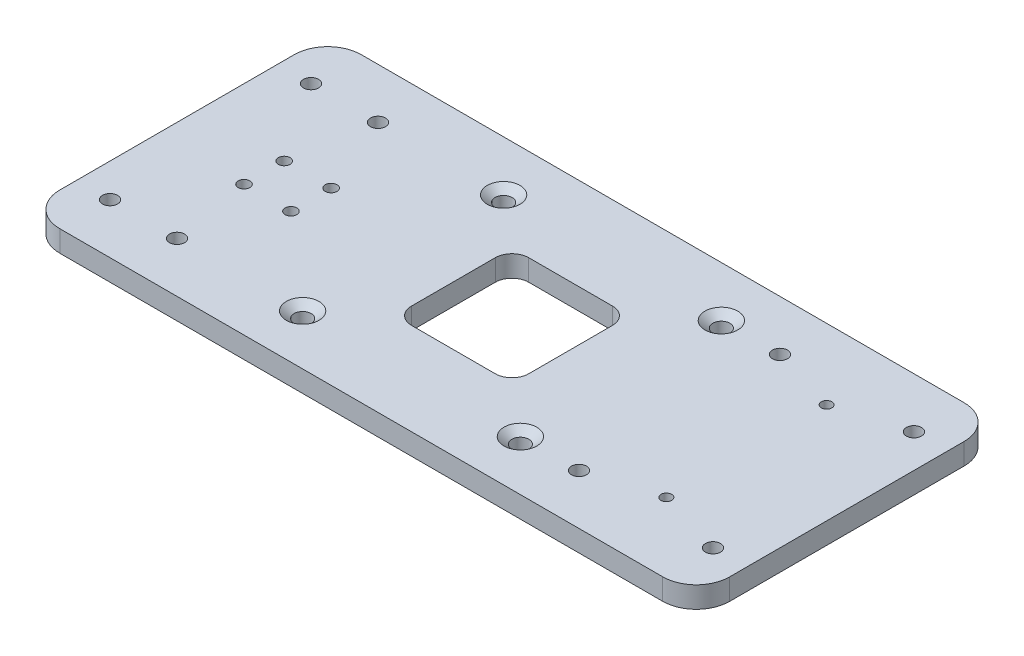
SolidWorks part; units mm, degrees
ref_plane "Front Plane" through (0, 0, 0) normal (0, 0, 1) x (1, 0, 0)
ref_plane "Top Plane" through (0, 0, 0) normal (0, 1, 0) x (1, 0, 0)
ref_plane "Right Plane" through (0, 0, 0) normal (1, 0, 0) x (0, 0, -1)
sketch "Sketch1" plane through (0, 0, 0) normal (0, 1, 0) x (1, 0, 0)
  line L1 (-100, -45) -> (100, -45)
  line L2 (-100, -45) -> (-100, 45)
  line L3 (-100, 45) -> (100, 45)
  line L4 (100, -45) -> (100, 45)
  line L5 (-100, -45) -> (100, 45) construction
  line L6 (-100, 45) -> (100, -45) construction
  point P0 (0, 0)
  dimension "D1" = 200
  dimension "D2" = 90
extrude "Boss-Extrude1" add sketch "Sketch1" along normal blind 6.35
sketch "Sketch2" plane through (0, 6.35, 0) normal (0, 1, 0) x (1, 0, 0)
  point P0 (-32.5, -30)
  point P2 (32.5, -30)
  point P5 (32.5, 30)
  point P6 (-32.5, 30)
  dimension "D1" = 30
  dimension "D2" = 32.5
  dimension "D3" = 2
  dimension "D4" = 2
hole_wizard "CSK for #10 Flat Head Machine Screw (100)1" positions "Sketch3" profile "Sketch5" countersink size "#10" standard "ANSI Inch" end condition through all
sketch "Sketch3" plane through (0, 6.35, 0) normal (0, 1, 0) x (1, 0, 0)
  point P0 (-32.5, 30)
  point P3 (-32.5, -30)
  point P6 (32.5, -30)
  point P9 (32.5, 30)
sketch "Sketch5" plane through (-32.5, 6.35, -30) normal (1, 0, 0) x (0, 0, 1)
  line L0 (0, 0) -> (0, 6.35)
  line L1 (0, 6.35) -> (2.5527, 6.35)
  line L2 (2.5527, 6.35) -> (2.5527, 1.9608)
  line L3 (2.5527, 1.9608) -> (4.8895, 0)
  line L5 (4.8895, 0) -> (0, 0)
  line L6 (-2.5527, 1.9608) -> (-4.8895, 0) construction
  line L11 (0, -6.35) -> (0, 107.95) construction
  dimension "Thru Hole Dia." = 5.1054
  dimension "Thru Hole Depth" = 6.35
  dimension "Near C'Sink Dia." = 9.779
  dimension "Near C'Sink Angle" = 100
sketch "Sketch6" plane through (0, 6.35, 0) normal (0, 1, 0) x (1, 0, 0)
  point P0 (-90, -30)
  point P1 (-70, -30)
  point P3 (50, -30)
  point P5 (90, -30)
  point P6 (90, 30)
  point P7 (-90, 30)
  point P9 (50, 30)
  point P10 (-70, 30)
  dimension "D1" = 90
  dimension "D4" = 180
  dimension "D5" = 70
  dimension "D2" = 2
  dimension "D3" = 2
  dimension "D6" = 2
  dimension "D7" = 2
hole_wizard "M4 Clearance Hole1" positions "Sketch7" profile "Sketch8" hole size "M4" standard "ANSI Metric" end condition through all
sketch "Sketch7" plane through (0, 6.35, 0) normal (0, 1, 0) x (1, 0, 0)
  point P0 (-90, -30)
  point P3 (-90, 30)
  point P6 (90, 30)
  point P9 (90, -30)
  point P13 (-70, -30)
  point P16 (-70, 30)
  point P19 (50, 30)
  point P22 (50, -30)
sketch "Sketch8" plane through (-90, 6.35, 30) normal (1, 0, 0) x (0, 0, 1)
  line L0 (0, 0) -> (0, 6.35)
  line L1 (0, 6.35) -> (2.25, 6.35)
  line L2 (2.25, 6.35) -> (2.25, 0)
  line L5 (2.25, 0) -> (0, 0)
  line L11 (0, -6.35) -> (0, 107.95) construction
  dimension "Thru Hole Dia." = 4.5
  dimension "Thru Hole Depth" = 6.35
sketch "Sketch9" plane through (0, 6.35, 0) normal (0, 1, 0) x (1, 0, 0)
  line L1 (-17.5, -17.5) -> (17.5, -17.5)
  line L2 (-17.5, -17.5) -> (-17.5, 17.5)
  line L3 (-17.5, 17.5) -> (17.5, 17.5)
  line L4 (17.5, -17.5) -> (17.5, 17.5)
  line L5 (-17.5, -17.5) -> (17.5, 17.5) construction
  line L6 (-17.5, 17.5) -> (17.5, -17.5) construction
  point P0 (0, 0)
  dimension "D1" = 35
  dimension "D2" = 35
extrude "Cut-Extrude1" cut sketch "Sketch9" against normal blind 6.35
fillet "Fillet1" radius 10 4 edges at (100, 3.175, 45) (-100, 3.175, -45) (100, 3.175, -45) (-100, 3.175, 45)
fillet "Fillet2" radius 5 4 edges at (17.5, 3.175, 17.5) (-17.5, 3.175, 17.5) (-17.5, 3.175, -17.5) (17.5, 3.175, -17.5)
sketch "Sketch10" plane through (100, 0, 0) normal (1, 0, 0) x (0, 0, -1)
  line L0 (-30, 6.35) -> (-30, 25.0076) construction
  line L1 (30, 6.35) -> (30, 25.55) construction
sketch "Sketch11" plane through (0, 0, 0) normal (0, -1, 0) x (1, 0, 0)
  line L0 (100, 35) -> (100, -35) construction
  line L1 (90, -45) -> (-90, -45) construction
  line L2 (100, 0) -> (18.944, 0) construction
  circle A0 centre (70, -23.9235) radius 1.675
  circle A2 centre (70, 23.9235) radius 1.675
  dimension "D2" = 21.0765
  dimension "D3" = 3.35
  dimension "D1" = 30
hole_wizard "#8-32 Tapped Hole1" positions "Sketch12" profile "Sketch13" tap size "#8-32" standard "ANSI Inch" end condition through all
sketch "Sketch12" plane through (0, 6.35, 0) normal (0, 1, 0) x (1, 0, 0)
  point P0 (70, 23.9235)
  point P3 (70, -23.9235)
sketch "Sketch13" plane through (70, 6.35, -23.9235) normal (1, 0, 0) x (0, 0, 1)
  line L0 (0, 0) -> (0, 6.35)
  line L1 (0, 6.35) -> (1.5875, 6.35)
  line L2 (1.5875, 6.35) -> (1.5875, 0)
  line L5 (1.5875, 0) -> (0, 0)
  line L11 (0, -6.35) -> (0, 107.95) construction
  dimension "Thru Tap Drill Dia." = 3.175
  dimension "Thru Tap Drill Depth" = 6.35
cosmetic thread "Hole Thread1" parameters "D2"=4.1656
cosmetic thread "Hole Thread2" parameters "D2"=4.1656
sketch "Sketch15" plane through (0, 0, 0) normal (0, -1, 0) x (-1, 0, 0)
  line L0 (74, -6) -> (60, 6) construction
  line L1 (67, 0) -> (100, 0) construction
  line L2 (100, 35) -> (100, -35) construction
  circle A0 centre (74, 6) radius 1.75
  circle A1 centre (60, 6) radius 1.75
  circle A2 centre (60, -6) radius 1.75
  circle A3 centre (74, -6) radius 1.75
  point P12 (67.0079, 0)
  point P13 (74, -5.7515)
  dimension "D6" = 3.5
  dimension "D3" = 12
  dimension "D4" = 14
  dimension "D5" = 26
  dimension "D1" = 2
  dimension "D2" = 2
extrude "Cut-Extrude2" cut sketch "Sketch15" against normal through all
